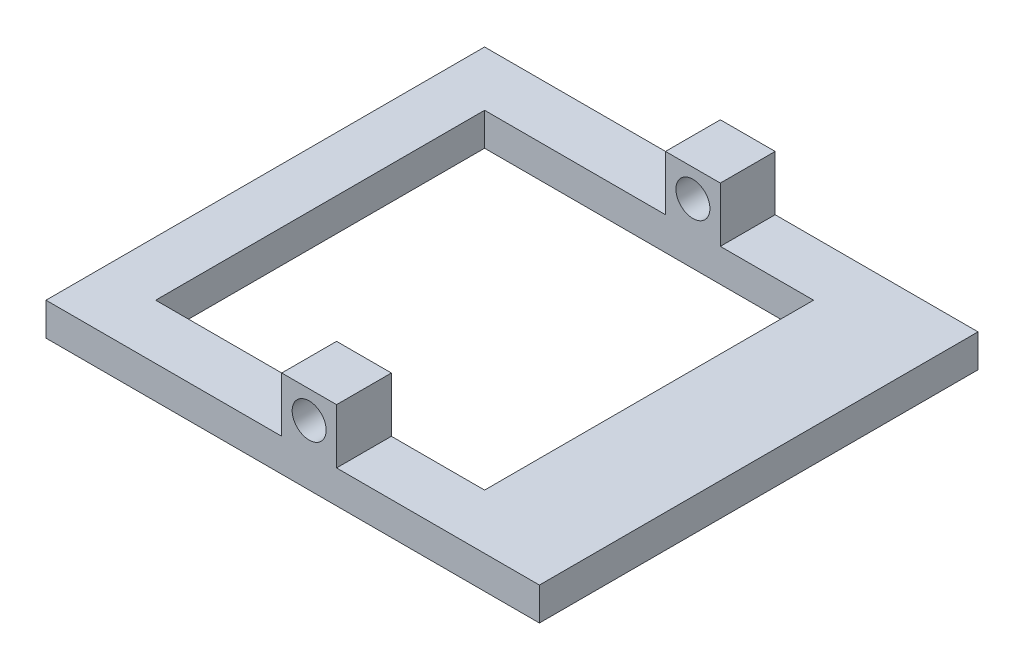
SolidWorks part; units mm, degrees
ref_plane "前视基准面" through (0, 0, 0) normal (0, 0, 1) x (1, 0, 0)
ref_plane "上视基准面" through (0, 0, 0) normal (0, 1, 0) x (1, 0, 0)
ref_plane "右视基准面" through (0, 0, 0) normal (1, 0, 0) x (0, 0, -1)
sketch "草图1" plane through (0, 0, 0) normal (0, 1, 0) x (1, 0, 0)
  line L1 (-22.5, 20) -> (22.5, 20)
  line L2 (-22.5, 20) -> (-22.5, -20)
  line L3 (-22.5, -20) -> (22.5, -20)
  line L4 (22.5, 20) -> (22.5, -20)
  line L5 (-22.5, 20) -> (22.5, -20) construction
  line L6 (-22.5, -20) -> (22.5, 20) construction
  line L11 (-17.5, 15) -> (12.5, 15)
  line L12 (-17.5, 15) -> (-17.5, -15)
  line L13 (-17.5, -15) -> (12.5, -15)
  line L14 (12.5, 15) -> (12.5, -15)
  line L15 (-17.5, 15) -> (12.5, -15) construction
  line L16 (-17.5, -15) -> (12.5, 15) construction
  point P0 (0, 0)
  point P6 (-2.5, 0)
  dimension "D1" = 45
  dimension "D2" = 40
  dimension "D3" = 30
  dimension "D4" = 30
  dimension "D5" = 5
  dimension "D6" = 20
extrude "凸台-拉伸2" add sketch "草图1" along normal blind 3
sketch "草图2" plane through (0, 0, -15) normal (0, 0, 1) x (1, 0, 0)
  line L0 (12.5, 0) -> (15.5, 0)
  line L1 (12.5, 3) -> (12.5, 0)
  line L2 (15.5, 0) -> (15.5, 2.1962)
  line L3 (15.5, 2.1962) -> (12.5, 3)
  dimension "D1" = 75
extrude "切除-拉伸2" cut sketch "草图2" along normal blind 30
sketch "草图3" plane through (0, 0, 20) normal (0, 0, 1) x (1, 0, 0)
  line L0 (-22.5, 3) -> (22.5, 3) construction
  line L1 (-1, 8) -> (4, 8)
  line L2 (-1, 8) -> (-1, 3)
  line L3 (-1, 3) -> (4, 3)
  line L4 (4, 8) -> (4, 3)
  line L5 (-1, 8) -> (4, 3) construction
  line L6 (-1, 3) -> (4, 8) construction
  line L9 (-17.5, 3) -> (-17.5, 0) construction
  circle A0 centre (1.5, 5.5) radius 1.55
  point P0 (1.5, 5.5)
  dimension "D3" = 3.1
  dimension "D1" = 5
  dimension "D2" = 5
  dimension "D4" = 19
extrude "凸台-拉伸3" add sketch "草图3" against normal blind 5
ref_plane "基准面4" through (0, 0, 0) normal (0, 0, -1) x (-1, 0, 0)
mirror "镜向2" about plane through (0, 0, 0) normal (0, 0, -1) of "凸台-拉伸3"
